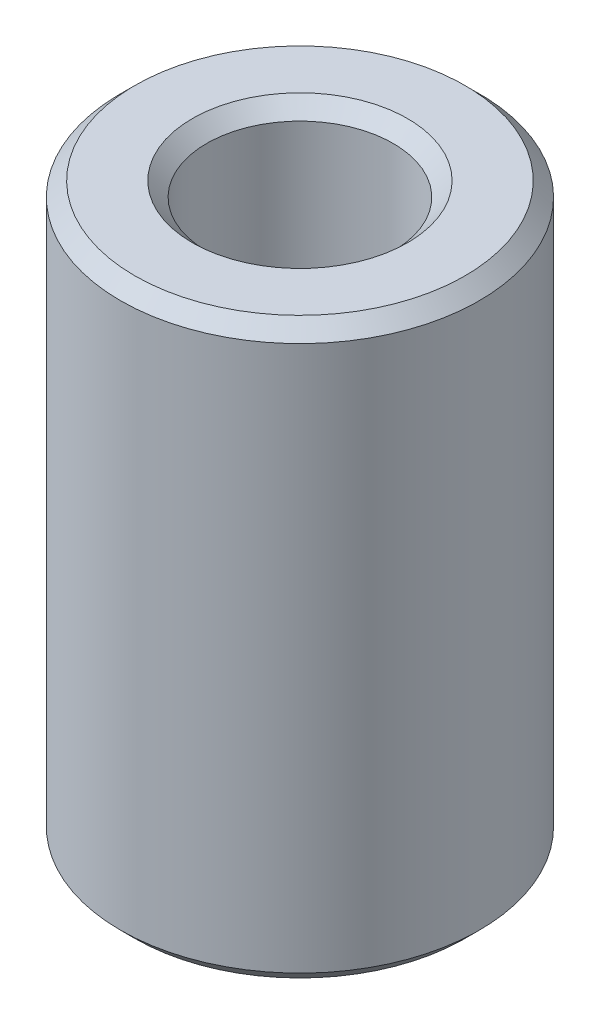
SolidWorks part; units mm, degrees
ref_plane "Ebene vorne" through (0, 0, 0) normal (0, 0, 1) x (1, 0, 0)
ref_plane "Ebene oben" through (0, 0, 0) normal (0, 1, 0) x (1, 0, 0)
ref_plane "Ebene rechts" through (0, 0, 0) normal (1, 0, 0) x (0, 0, -1)
sketch "Skizze1" plane through (0, 0, 0) normal (0, 1, 0) x (1, 0, 0)
  circle A0 centre (0, 0) radius 2.5
  circle A1 centre (0, 0) radius 1.3
  dimension "D1" = 2.6
  dimension "D2" = 5
extrude "Aufsatz-Linear austragen1" add sketch "Skizze1" along normal blind 8
chamfer "Fase1" distance 0.2 angle 45 4 edges at (0, 0, 2.5) (0, 0, 1.3) (0, 8, 2.5) (0, 8, 1.3)
